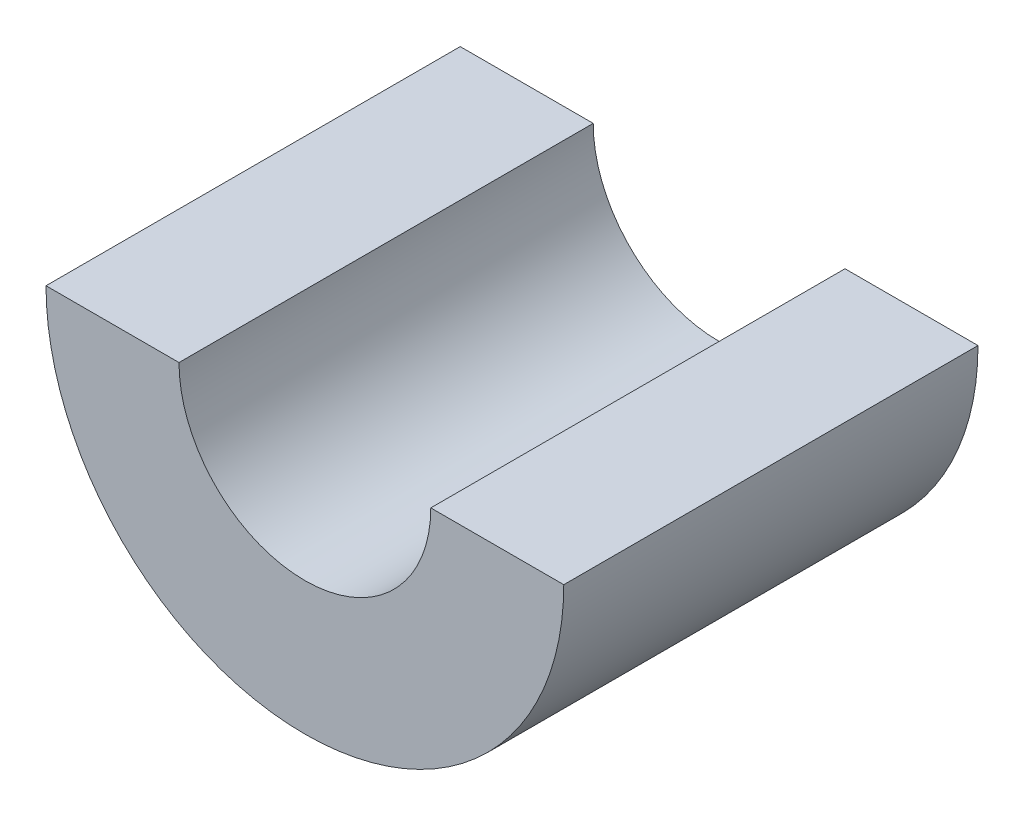
SolidWorks part; units mm, degrees
material "ABS"
ref_plane "Front Plane" through (0, 0, 0) normal (0, 0, 1) x (1, 0, 0)
ref_plane "Top Plane" through (0, 0, 0) normal (0, 1, 0) x (1, 0, 0)
ref_plane "Right Plane" through (0, 0, 0) normal (1, 0, 0) x (0, 0, -1)
sketch "Sketch1" plane through (0, 0, 0) normal (0, 0, 1) x (1, 0, 0)
  line L0 (-2.4314, 0) -> (2.4314, 0)
  line L1 (-5, 0) -> (5, 0)
  circle A0 centre (0, 0) radius 2.4314
  circle A1 centre (0, 0) radius 1.9314
  circle A2 centre (-0.8, -0.8) radius 0.8
  circle A3 centre (0.8, -0.8) radius 0.8
  circle A4 centre (0, 0) radius 5
  dimension "D1" = 1.6
  dimension "D2" = 0.5
  dimension "D3" = 10
extrude "Boss-Extrude1" add sketch "Sketch1" along normal blind 8 contours L1 A4 A0
